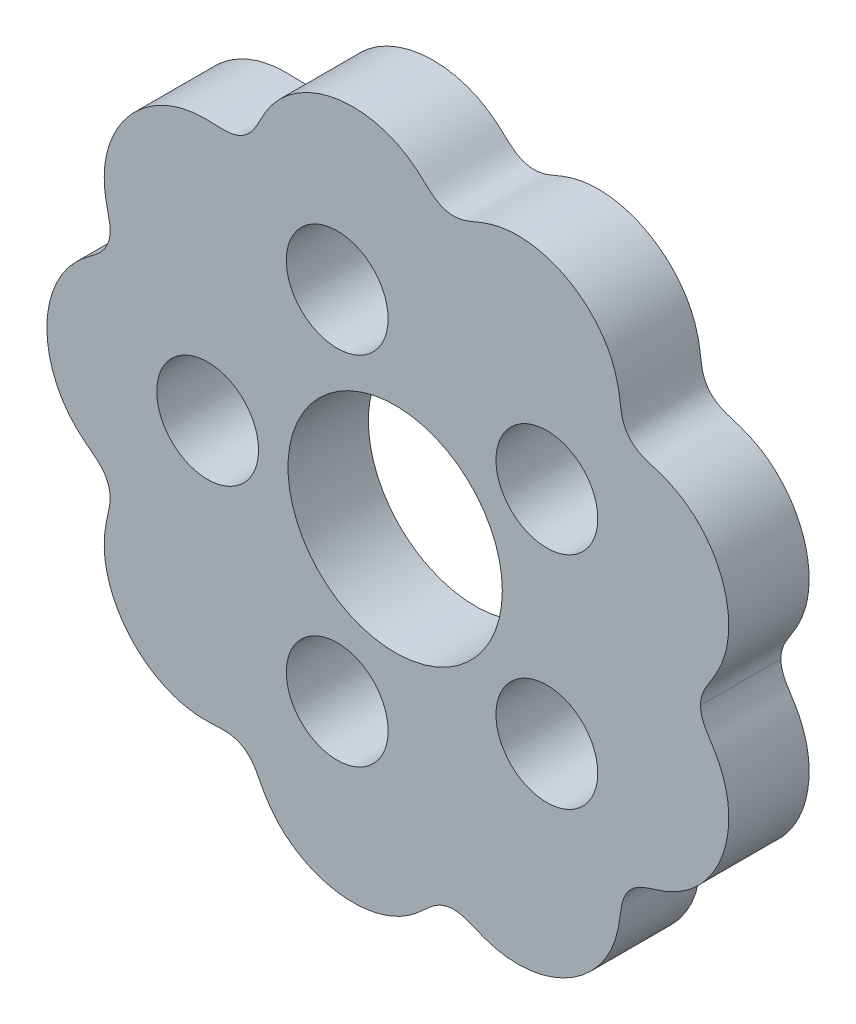
SolidWorks part; units mm, degrees
ref_plane "前视基准面" through (0, 0, 0) normal (0, 0, 1) x (1, 0, 0)
ref_plane "上视基准面" through (0, 0, 0) normal (0, 1, 0) x (1, 0, 0)
ref_plane "右视基准面" through (0, 0, 0) normal (1, 0, 0) x (0, 0, -1)
sketch "草图1" plane through (0, 0, 0) normal (0, 0, 1) x (1, 0, 0)
  line L1 (0, 0) -> (-14.4114, 0) construction
  spline S0 degree 4 poles (11.1318, 6.0354) (11.2423, 5.9392) (11.4002, 5.7862) (11.5945, 5.5661) (11.8078, 5.2681) (11.96, 5.0176) (12.093, 4.7563) (12.2062, 4.4859) (12.299, 4.2079) (12.3709, 3.9237) (12.4214, 3.6349) (12.4501, 3.3431) (12.4565, 3.0501) (12.4401, 2.7571) (12.4061, 2.5035) (12.3618, 2.2867) (12.3169, 2.1127) (12.2733, 1.9701) (12.219, 1.8174) (12.184, 1.7283) (12.1288, 1.6007) (12.0729, 1.4821) (12.0032, 1.3474) (11.9129, 1.1889) (11.7985, 1.0059) (11.6647, 0.8015) (11.5407, 0.5894) (11.4461, 0.3623) (11.3971, 0.1284) (11.3956, -0.1024) (11.4364, -0.3212) (11.5103, -0.5225) (11.6103, -0.7117) (11.7241, -0.8925) (11.8694, -1.1164) (12.075, -1.4609) (12.2931, -1.952) (12.45, -2.6072) (12.4748, -3.3609) (12.3538, -4.105) (12.0943, -4.8126) (11.706, -5.4586) (11.1999, -6.0173) (10.6571, -6.4158) (10.1247, -6.6723) (9.6418, -6.8289) (9.2306, -6.9464) (8.8529, -7.1604) (8.5749, -7.4999) (8.439, -7.9119) (8.3969, -8.3374) (8.323, -8.8403) (8.1582, -9.4081) (7.8549, -10.0099) (7.3877, -10.602) (6.8136, -11.0935) (6.1557, -11.4683) (5.4367, -11.7116) (4.7767, -11.7981) (4.2077, -11.7749) (3.7321, -11.6875) (3.3489, -11.5727) (2.9706, -11.4168) (2.5851, -11.2479) (2.1623, -11.1767) (1.7362, -11.2622) (1.3709, -11.4923) (1.066, -11.7913) (0.6882, -12.1256) (0.2029, -12.4497) (-0.4055, -12.7122) (-1.1287, -12.8662) (-2.0601, -12.8836) (-2.9774, -12.6677) (-3.8153, -12.2256) (-4.4445, -11.6352) (-4.7945, -11.1587) (-5.0365, -10.7115) (-5.2213, -10.326) (-5.4873, -9.9855) (-5.8598, -9.7611) (-6.2818, -9.6854) (-6.7017, -9.7127) (-7.2052, -9.7335) (-7.7937, -9.6793) (-8.4448, -9.4944) (-9.1196, -9.1427) (-9.7112, -8.667) (-10.2004, -8.0892) (-10.5707, -7.4304) (-10.8061, -6.7139) (-10.8841, -6.0446) (-10.8439, -5.4548) (-10.7406, -4.9572) (-10.6351, -4.543) (-10.6238, -4.1091) (-10.7709, -3.6958) (-11.054, -3.3667) (-11.4007, -3.1163) (-11.7264, -2.8608) (-12.0158, -2.582) (-12.2639, -2.2833) (-12.4725, -1.9713) (-12.6478, -1.6396) (-12.7891, -1.292) (-12.8956, -0.9323) (-12.9669, -0.564) (-13.0103, -0.113) (-12.9966, 0.419) (-12.9063, 0.9361) (-12.7431, 1.4263) (-12.578, 1.7752) (-12.4493, 1.9995) (-12.344, 2.1597) (-12.2699, 2.2632) (-12.2006, 2.3528) (-12.1421, 2.4249) (-12.0819, 2.496) (-12.0293, 2.5548) (-11.944, 2.6449) (-11.8509, 2.7373) (-11.7389, 2.8403) (-11.5992, 2.9588) (-11.4285, 3.092) (-11.2321, 3.2389) (-11.0426, 3.3966) (-10.8761, 3.5791) (-10.7171, 3.8379) (-10.6336, 4.1305) (-10.6319, 4.4298) (-10.6923, 4.7767) (-10.7775, 5.1182) (-10.8289, 5.4073) (-10.8504, 5.6412) (-10.8559, 5.7583) knots 0 0 0 0 0 0.010549 0.015824 0.021099 0.026373 0.031648 0.036923 0.042197 0.047472 0.052747 0.058021 0.063296 0.068571 0.073845 0.076483 0.07912 0.081757 0.084395 0.086601 0.088808 0.091015 0.093222 0.097635 0.102049 0.106462 0.110876 0.115289 0.119703 0.123549 0.127396 0.131243 0.135089 0.138936 0.142782 0.150475 0.16397 0.177465 0.19096 0.204455 0.217945 0.231435 0.244925 0.258415 0.266105 0.273795 0.281485 0.289175 0.29687 0.304565 0.312261 0.319956 0.333454 0.346953 0.360451 0.37395 0.387562 0.401174 0.414786 0.421592 0.428398 0.435961 0.443523 0.451085 0.458647 0.466336 0.474025 0.481714 0.489403 0.502639 0.515874 0.52911 0.542345 0.569346 0.582846 0.596346 0.604042 0.611738 0.619435 0.627131 0.634694 0.642257 0.64982 0.657384 0.670998 0.684612 0.698225 0.711839 0.725336 0.738833 0.75233 0.765826 0.773521 0.781215 0.788909 0.796603 0.804294 0.811985 0.819676 0.827368 0.834113 0.840859 0.847605 0.854351 0.861096 0.867842 0.874588 0.881334 0.893692 0.90605 0.912229 0.918409 0.921498 0.924588 0.926133 0.927677 0.929222 0.930767 0.932982 0.935197 0.937412 0.939626 0.944056 0.948486 0.952916 0.957346 0.961775 0.966205 0.974654 0.978878 0.983103 0.991551 1 1 1 1 1 construction
  spline S1 degree 4 poles (11.4, 0) (11.4, -0.0007) (11.4, -0.0548) (11.4067, -0.1622) (11.4364, -0.3212) (11.5103, -0.5225) (11.6103, -0.7117) (11.7241, -0.8925) (11.8694, -1.1164) (12.075, -1.4609) (12.2931, -1.952) (12.45, -2.6072) (12.4748, -3.3609) (12.3538, -4.105) (12.0943, -4.8126) (11.706, -5.4586) (11.1999, -6.0173) (10.6571, -6.4158) (10.1247, -6.6723) (9.6418, -6.8289) (9.2306, -6.9464) (8.8529, -7.1604) (8.5749, -7.4999) (8.439, -7.9119) (8.3969, -8.3374) (8.323, -8.8403) (8.1582, -9.4081) (7.8549, -10.0099) (7.3877, -10.602) (6.8136, -11.0935) (6.1557, -11.4683) (5.4367, -11.7116) (4.7767, -11.7981) (4.2077, -11.7749) (3.7321, -11.6875) (3.3489, -11.5727) (2.9706, -11.4168) (2.5851, -11.2479) (2.1623, -11.1767) (1.7362, -11.2622) (1.3709, -11.4923) (1.066, -11.7913) (0.6882, -12.1256) (0.2029, -12.4497) (-0.4055, -12.7122) (-1.1287, -12.8662) (-2.0601, -12.8836) (-2.9774, -12.6677) (-3.8153, -12.2256) (-4.4445, -11.6352) (-4.7945, -11.1587) (-5.0365, -10.7115) (-5.2213, -10.326) (-5.4873, -9.9855) (-5.8598, -9.7611) (-6.2818, -9.6854) (-6.7017, -9.7127) (-7.2052, -9.7335) (-7.7937, -9.6793) (-8.4448, -9.4944) (-9.1196, -9.1427) (-9.7112, -8.667) (-10.2004, -8.0892) (-10.5707, -7.4304) (-10.8061, -6.7139) (-10.8841, -6.0446) (-10.8439, -5.4548) (-10.7406, -4.9572) (-10.6351, -4.543) (-10.6238, -4.1091) (-10.7709, -3.6958) (-11.054, -3.3667) (-11.4007, -3.1163) (-11.7264, -2.8608) (-12.0158, -2.582) (-12.2639, -2.2833) (-12.4725, -1.9713) (-12.6478, -1.6396) (-12.7891, -1.292) (-12.8956, -0.9323) (-12.9669, -0.564) (-12.9939, -0.2832) (-13, -0.0952) (-13, -0.0008) (-13, 0) knots 0.119653 0.119653 0.119653 0.119653 0.119653 0.119703 0.123549 0.127396 0.131243 0.135089 0.138936 0.142782 0.150475 0.16397 0.177465 0.19096 0.204455 0.217945 0.231435 0.244925 0.258415 0.266105 0.273795 0.281485 0.289175 0.29687 0.304565 0.312261 0.319956 0.333454 0.346953 0.360451 0.37395 0.387562 0.401174 0.414786 0.421592 0.428398 0.435961 0.443523 0.451085 0.458647 0.466336 0.474025 0.481714 0.489403 0.502639 0.515874 0.52911 0.542345 0.569346 0.582846 0.596346 0.604042 0.611738 0.619435 0.627131 0.634694 0.642257 0.64982 0.657384 0.670998 0.684612 0.698225 0.711839 0.725336 0.738833 0.75233 0.765826 0.773521 0.781215 0.788909 0.796603 0.804294 0.811985 0.819676 0.827368 0.834113 0.840859 0.847605 0.854351 0.861096 0.867842 0.874588 0.881334 0.881389 0.881389 0.881389 0.881389 0.881389
  spline S2 degree 4 poles (11.4, 0) (11.4, 0.0007) (11.4, 0.0548) (11.4067, 0.1623) (11.4364, 0.3212) (11.5103, 0.5225) (11.6103, 0.7117) (11.7241, 0.8925) (11.8694, 1.1165) (12.075, 1.4609) (12.2931, 1.952) (12.45, 2.6072) (12.4748, 3.3609) (12.3538, 4.1051) (12.0943, 4.8126) (11.706, 5.4586) (11.1999, 6.0173) (10.6571, 6.4158) (10.1247, 6.6723) (9.6418, 6.8289) (9.2306, 6.9464) (8.8529, 7.1604) (8.5749, 7.4999) (8.439, 7.9119) (8.3969, 8.3374) (8.323, 8.8403) (8.1582, 9.4081) (7.8549, 10.0099) (7.3877, 10.602) (6.8136, 11.0936) (6.1557, 11.4683) (5.4367, 11.7116) (4.7767, 11.7981) (4.2077, 11.7749) (3.7321, 11.6875) (3.3488, 11.5728) (2.9706, 11.4168) (2.5851, 11.2479) (2.1623, 11.1768) (1.7362, 11.2622) (1.3709, 11.4923) (1.066, 11.7913) (0.6882, 12.1256) (0.2029, 12.4497) (-0.4055, 12.7122) (-1.1287, 12.8662) (-2.0601, 12.8836) (-2.9774, 12.6677) (-3.8154, 12.2256) (-4.4445, 11.6352) (-4.7945, 11.1587) (-5.0365, 10.7115) (-5.2213, 10.3261) (-5.4873, 9.9856) (-5.8598, 9.7611) (-6.2819, 9.6854) (-6.7017, 9.7127) (-7.2052, 9.7335) (-7.7937, 9.6793) (-8.4448, 9.4944) (-9.1196, 9.1427) (-9.7112, 8.667) (-10.2004, 8.0892) (-10.5707, 7.4304) (-10.8061, 6.7139) (-10.8841, 6.0446) (-10.8439, 5.4548) (-10.7406, 4.9572) (-10.6351, 4.543) (-10.6238, 4.1091) (-10.7709, 3.6958) (-11.054, 3.3667) (-11.4007, 3.1163) (-11.7264, 2.8608) (-12.0158, 2.582) (-12.2639, 2.2833) (-12.4725, 1.9713) (-12.6478, 1.6396) (-12.7891, 1.292) (-12.8956, 0.9323) (-12.9669, 0.564) (-12.9939, 0.2832) (-13, 0.0952) (-13, 0.0008) (-13, 0) knots 0.119653 0.119653 0.119653 0.119653 0.119653 0.119703 0.123549 0.127396 0.131243 0.135089 0.138936 0.142782 0.150475 0.16397 0.177465 0.19096 0.204455 0.217945 0.231435 0.244925 0.258415 0.266105 0.273795 0.281485 0.289175 0.29687 0.304565 0.312261 0.319956 0.333454 0.346953 0.360451 0.37395 0.387562 0.401174 0.414786 0.421592 0.428398 0.435961 0.443523 0.451085 0.458647 0.466336 0.474025 0.481714 0.489403 0.502639 0.515874 0.52911 0.542345 0.569346 0.582846 0.596346 0.604042 0.611738 0.619435 0.627131 0.634694 0.642257 0.64982 0.657384 0.670998 0.684612 0.698225 0.711839 0.725336 0.738833 0.75233 0.765826 0.773521 0.781215 0.788909 0.796603 0.804294 0.811985 0.819676 0.827368 0.834113 0.840859 0.847605 0.854351 0.861096 0.867842 0.874588 0.881334 0.881389 0.881389 0.881389 0.881389 0.881389
extrude "凸台-拉伸1" add sketch "草图1" along normal blind 3
sketch "草图3" plane through (0, 0, 3) normal (0, 0, 1) x (1, 0, 0)
  circle A0 centre (0, 0) radius 4
extrude "切除-拉伸1" cut sketch "草图3" against normal blind 3
sketch "草图4" plane through (0, 0, 3) normal (0, 0, 1) x (1, 0, 0)
  circle A0 centre (-7, 0) radius 1.9
  circle A2 centre (-2.1631, 6.6574) radius 1.9
  circle A3 centre (5.6631, 4.1145) radius 1.9
  circle A4 centre (5.6631, -4.1145) radius 1.9
  circle A5 centre (-2.1631, -6.6574) radius 1.9
  point P14 (0, 0)
  dimension "D1" = 5
extrude "切除-拉伸2" cut sketch "草图4" against normal blind 3
